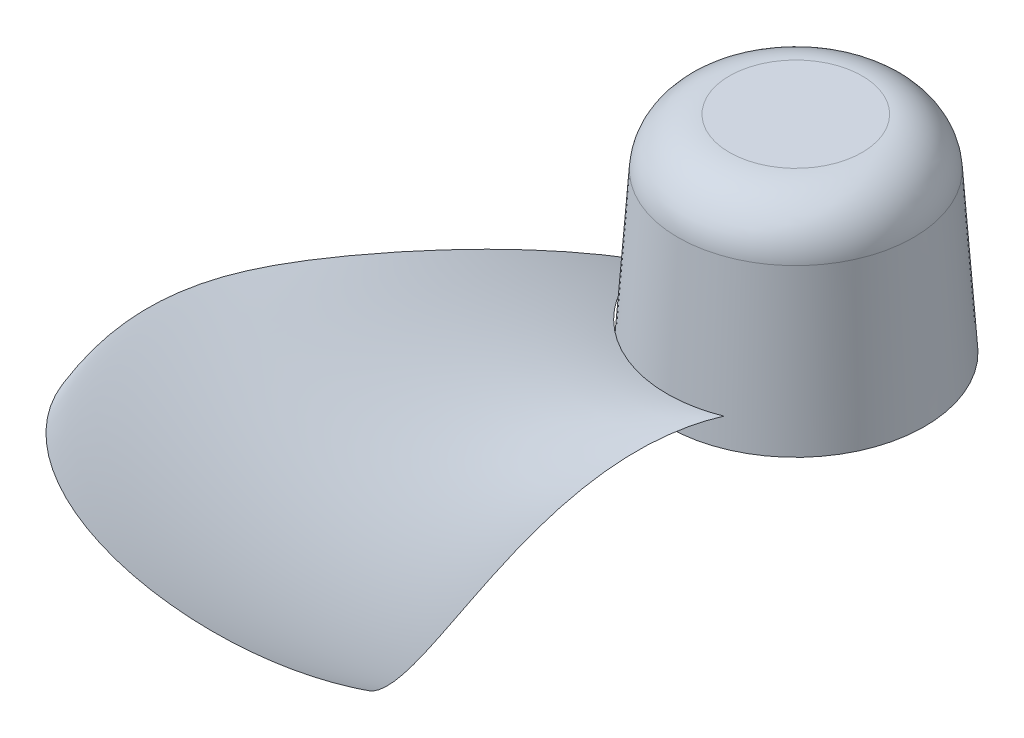
SolidWorks part; units mm, degrees
ref_plane "Płaszczyzna przednia" through (0, 0, 0) normal (0, 0, 1) x (1, 0, 0)
ref_plane "Płaszczyzna górna" through (0, 0, 0) normal (0, 1, 0) x (1, 0, 0)
ref_plane "Płaszczyzna prawa" through (0, 0, 0) normal (1, 0, 0) x (0, 0, -1)
sketch "Szkic1" plane through (0, 0, 0) normal (0, 1, 0) x (1, 0, 0)
  circle A0 centre (0, 0) radius 50
  dimension "D1" = 100
extrude "Dodanie-wyciągnięcie1" add sketch "Szkic1" along normal blind 80 draft 4
fillet "Zaokrąglenie1" radius 20 1 edges at (0, 80, 44.4059)
sketch "Szkic3" plane through (0, 0, 0) normal (0, 0, 1) x (1, 0, 0)
  line L0 (0, 0) -> (0, 44) construction
  line L1 (0, 44) -> (-129.5, 104.3868) construction
  line L2 (-129.5, 104.3868) -> (-129.5, 0) construction
  line L3 (-129.5, 0) -> (0, 0) construction
  line L4 (0, 44) -> (-129.5, 44) construction
  dimension "D1" = 44
  dimension "D2" = 25
  dimension "D3" = 129.5
ref_plane "Płaszczyzna1" through (0, 0, 200) normal (0, 0, 1) x (1, 0, 0)
sketch "Szkic4" plane through (0, 0, 200) normal (0, 0, 1) x (1, 0, 0)
  line L0 (0, 0) -> (0, 33.9609) construction
  spline S0 degree 2 poles (-126.4133, 53.0488) (-63.641, 3.2298) (0, 0) knots 0 0 0 0.783473 0.783473 0.783473 construction
ref_plane "Płaszczyzna2" through (0, 0, 10) normal (0, 0, 1) x (1, 0, 0)
sketch "Szkic5" plane through (0, 0, 0) normal (0, 1, 0) x (1, 0, 0)
  spline S0 degree 3 poles (-72.1437, -230.8619) (-81.2709, -204.0195) (-106.2115, -154.4365) (-70.3813, -79.3668) (-45.0124, -6.4179) knots 0 0 0 0 0.652527 1 1 1 1
ref_plane "Płaszczyzna3" through (0, 0, 200) normal (0, 0, 1) x (1, 0, 0)
ref_plane "Płaszczyzna4" through (0, 0, 10) normal (0, 0, 1) x (1, 0, 0)
sketch "Szkic6" plane through (0, 0, 200) normal (0, 0, 1) x (1, 0, 0)
  line L0 (-31.6773, -6.9595) -> (-31.6773, 26.7365) construction
  spline S0 degree 2 poles (-150.2948, 45.8243) (-95.3183, -3.7297) (-31.6773, -6.9595) knots 0 0 0 0.783473 0.783473 0.783473 construction
sketch "Szkic7" plane through (0, 0, 10) normal (0, 0, 1) x (1, 0, 0)
  line L0 (-47.0003, 10.8581) -> (-47.0003, 85.3345) construction
  spline S0 degree 2 poles (30.6638, 19.1172) (-9.4128, 1.7617) (-47.0003, 10.8581) knots 0 0 0 0.857133 0.857133 0.857133
ref_plane "Płaszczyzna5" through (-47.0003, 0, 0) normal (1, 0, 0) x (0, 0, -1)
ref_plane "Płaszczyzna6" through (0, 80, 0) normal (0, 1, 0) x (1, 0, 0)
sketch "Szkic8" plane through (-47.0003, 0, 0) normal (1, 0, 0) x (0, 0, -1)
  spline S0 degree 3 poles (-233.1025, 45.6432) (-164.566, 57.8727) (-69.7695, 42.3078) (-10, 10.8581) knots 0 0 0 0 0.899124 0.899124 0.899124 0.899124
curve "Krzywa1"
sketch3d "Szkic 3D3"
  line L0 (35.5644, 3.8139, 200) -> (90.875, 3.8139, 200) construction
  spline S0 degree 1 poles (-82.334, 49.2189, 202.2767) (35.5644, 3.8139, 200) knots 0 0 1 1 construction
  spline S2 degree 3 poles (-82.334, 49.2189, 202.2767) (-61.8236, 50.2579, 252.8817) (11.2768, 23.5537, 244.2628) (35.5644, 3.8139, 200) knots 0 0 0 0 0.886524 0.886524 0.886524 0.886524
  spline S3 degree 3 poles (-72.1437, 46.0316, 230.8619) (-73.7209, 46.8121, 226.2233) (-75.437, 47.4448, 221.6185) (-78.8336, 48.477, 212.3747) (-80.5167, 48.8758, 207.7366) (-83.6406, 49.4668, 198.3576) (-85.0863, 49.6589, 193.6014) (-87.5557, 49.8434, 184.0125) (-88.5775, 49.8361, 179.1925) (-90.0923, 49.6323, 169.4875) (-90.5858, 49.4357, 164.6025) (-90.9767, 48.8567, 154.7585) (-90.8688, 48.4703, 149.7662) (-90.0452, 47.5375, 139.9616) (-89.3351, 46.9913, 135.1297) (-87.3685, 45.7546, 125.5947) (-86.1002, 45.0646, 120.8939) (-83.2406, 43.5437, 111.5756) (-81.6552, 42.7113, 106.951) (-78.3963, 40.9109, 97.7958) (-76.7188, 39.9419, 93.2581) (-71.6737, 36.8173, 79.7204) (-68.2984, 34.446, 70.7934) (-61.7141, 29.0427, 53.0939) (-58.4957, 26.0128, 44.324) (-52.24, 19.1317, 26.9858) (-49.2005, 15.2866, 18.4161) (-46.2608, 10.8581, 10) knots 0 0 0 0 0.0625 0.0625 0.125 0.125 0.1875 0.1875 0.25 0.25 0.3125 0.3125 0.375 0.375 0.4375 0.4375 0.5 0.5 0.5625 0.5625 0.625 0.625 0.75 0.75 0.875 0.875 1 1 1 1 construction
sketch "Szkic10" plane through (0, 80, 0) normal (0, 1, 0) x (1, 0, 0)
  spline S0 degree 3 poles (-26.9689, 161.062) (-31.9643, 242.6638) (77.2652, 237.7429) (96.7539, 143.0972) (95.4784, 84.9518) (68.0164, 36.8289) (60.8766, 33.6036) (43.4937, 13.4714) (47.4631, 8.3676) knots 0 0 0 0 0.351826 0.591029 0.767928 0.89067 0.97965 1 1 1 1
ref_plane "Płaszczyzna7" through (0, 11, 0) normal (0, 1, 0) x (1, 0, 0)
sketch3d "Szkic 3D4"
  spline S1 degree 3 poles (-82.334, 49.2189, 202.2767) (-83.8605, 49.4966, 197.8586) (-85.2796, 49.6818, 193.3806) (-87.8134, 49.8785, 184.0894) (-88.9036, 49.8796, 179.2844) (-90.5569, 49.6913, 169.6017) (-91.1203, 49.5019, 164.724) (-91.6526, 48.9357, 154.8859) (-91.6168, 48.5551, 149.8921) (-90.9352, 47.6321, 140.0757) (-90.2952, 47.09, 135.2335) (-88.4675, 45.8598, 125.6701) (-87.268, 45.1723, 120.9509) (-84.5451, 43.6555, 111.5911) (-83.0278, 42.8247, 106.9435) (-79.904, 41.0272, 97.7407) (-78.2937, 40.0594, 93.1785) (-73.4495, 36.9385, 79.5667) (-70.2076, 34.5696, 70.5898) (-63.8894, 29.1711, 52.792) (-60.8038, 26.1438, 43.9738) (-54.8127, 19.268, 26.5402) (-51.9051, 15.4256, 17.9237) (-49.0967, 11, 9.4614) knots 0.12842 0.12842 0.12842 0.12842 0.1875 0.1875 0.25 0.25 0.3125 0.3125 0.375 0.375 0.4375 0.4375 0.5 0.5 0.5625 0.5625 0.625 0.625 0.75 0.75 0.875 0.875 1 1 1 1
sketch3d "Szkic 3D2"
  spline S0 degree 3 poles (35.5644, 3.8139, 200) (22.269, -19.0957, 163.9135) (-0.7699, 13.6896, 99.6051) (18.5275, 11, 46.4406) knots 0 0 0 0 1 1 1 1
sketch "Szkic13" plane through (0, 11, 0) normal (0, 1, 0) x (1, 0, 0)
  circle A0 centre (0, 0) radius 50 construction
  arc A1 (-49.0967, -9.4614) -> (18.5275, -46.4406) centre (0, 0) ccw
surface "Powierzchnia-wypełnij1"
